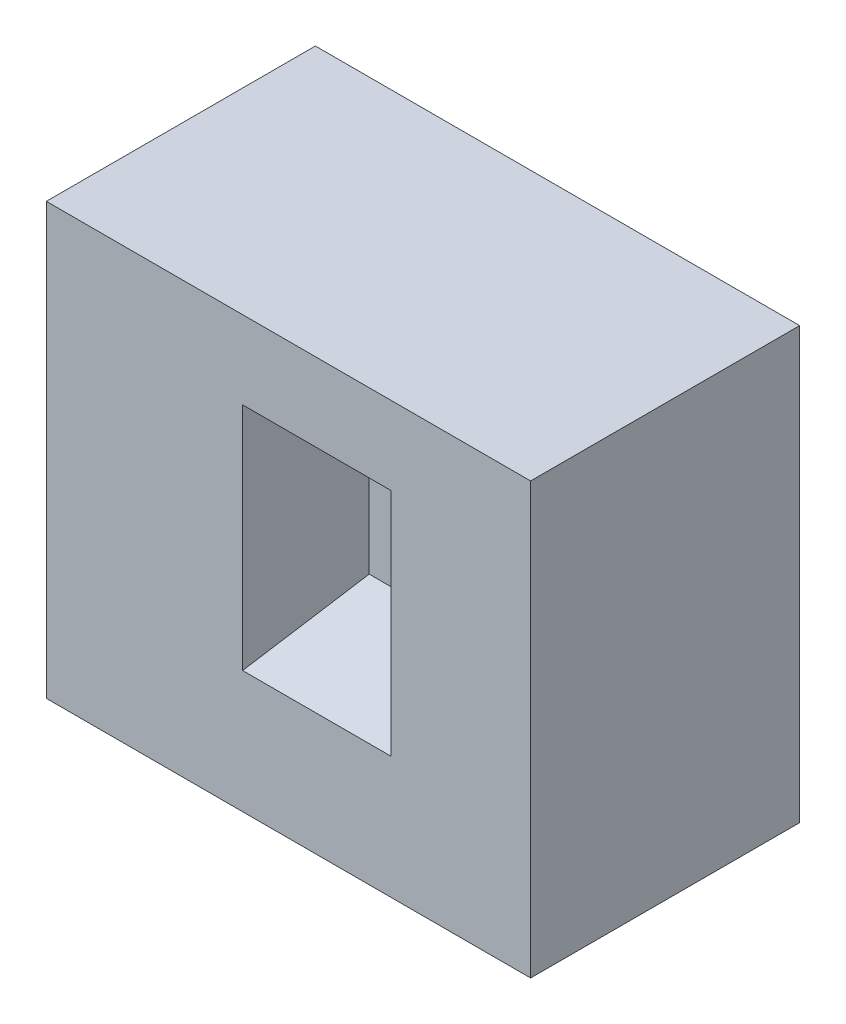
SolidWorks part; units mm, degrees
ref_plane "Front Plane" through (0, 0, 0) normal (0, 0, 1) x (1, 0, 0)
ref_plane "Top Plane" through (0, 0, 0) normal (0, 1, 0) x (1, 0, 0)
ref_plane "Right Plane" through (0, 0, 0) normal (1, 0, 0) x (0, 0, -1)
sketch "Sketch1" plane through (0, 0, 0) normal (0, 0, 1) x (1, 0, 0)
  line L1 (0, 0) -> (90, 0)
  line L2 (0, 0) -> (0, 80)
  line L3 (0, 80) -> (90, 80)
  line L4 (90, 0) -> (90, 80)
  dimension "D1" = 90
  dimension "D2" = 80
extrude "Base" add sketch "Sketch1" along normal mid plane 50
sketch "Sketch2" plane through (0, 0, 25) normal (0, 0, 1) x (1, 0, 0)
  line L1 (40, 30) -> (52.5059, 30)
  line L2 (40, 30) -> (40, 48.7043)
  line L3 (40, 48.7043) -> (52.5059, 48.7043)
  line L4 (52.5059, 30) -> (52.5059, 48.7043)
  point P7 (18.2746, 12.0056)
  dimension "D1" = 18.7043
  dimension "D2" = 12.5059
  dimension "D3" = 40
  dimension "D4" = 30
extrude "Pocket" cut sketch "Sketch2" against normal blind 20
draft "Draft10" type of draft neutral plane draft angle 10 faces to draft 1 face at (40, 39.3521, 15) neutral plane through (40, 48.7043, 5) neutral plane normal (0, 0, 1) parameters "D1"=10
draft "Draft20" type of draft neutral plane draft angle 20 faces to draft 1 face at (45.3713, 30, 15) neutral plane through (40, 48.7043, 5) neutral plane normal (0, 0, 1) parameters "D1"=20
draft "Draft30" type of draft neutral plane draft angle 30 faces to draft 1 face at (52.5059, 37.5323, 15) neutral plane through (40, 48.7043, 5) neutral plane normal (0, 0, 1) parameters "D1"=30
draft "Draft40" type of draft neutral plane draft angle 40 faces to draft 1 face at (48.2581, 48.7043, 15) neutral plane through (40, 48.7043, 5) neutral plane normal (0, 0, 1) parameters "D1"=40
